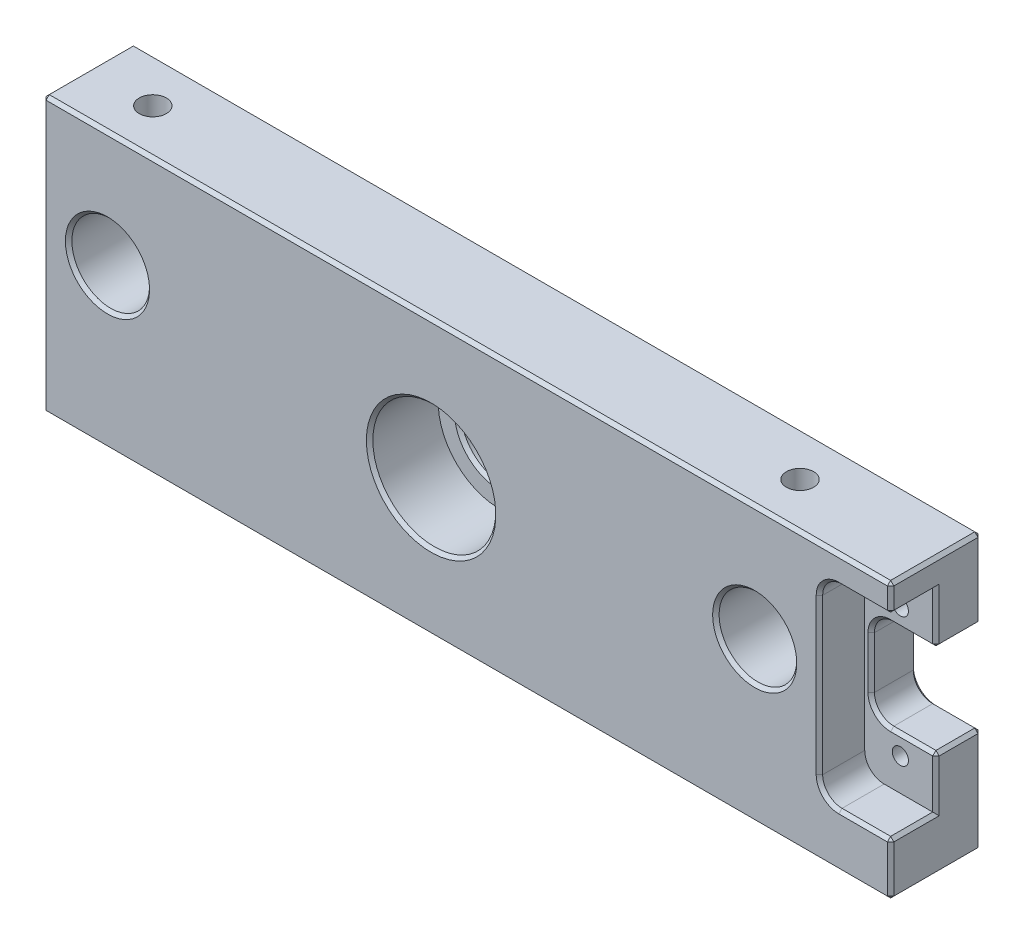
SolidWorks part; units mm, degrees
ref_plane "Front Plane" through (0, 0, 0) normal (0, 0, 1) x (1, 0, 0)
ref_plane "Top Plane" through (0, 0, 0) normal (0, 1, 0) x (1, 0, 0)
ref_plane "Right Plane" through (0, 0, 0) normal (1, 0, 0) x (0, 0, -1)
sketch "Sketch1" plane through (0, 0, 0) normal (0, 0, 1) x (1, 0, 0)
  line L1 (-60, -21.25) -> (60, -21.25)
  line L2 (-60, -21.25) -> (-60, 21.25)
  line L3 (-60, 21.25) -> (60, 21.25)
  line L4 (60, -21.25) -> (60, 21.25)
  line L5 (-60, -21.25) -> (60, 21.25) construction
  line L6 (-60, 21.25) -> (60, -21.25) construction
  point P0 (0, 0)
  dimension "D1" = 120
  dimension "D2" = 42.5
extrude "Boss-Extrude1" add sketch "Sketch1" along normal mid plane 14
sketch "Sketch2" plane through (0, 0, 7) normal (0, 0, 1) x (1, 0, 0)
  circle A0 centre (0, 0) radius 9.5
  dimension "D1" = 19
extrude "Cut-Extrude1" cut sketch "Sketch2" against normal blind 10.6
sketch "Sketch3" plane through (0, 0, -3.6) normal (0, 0, 1) x (1, 0, 0)
  circle A0 centre (0, 0) radius 6.5
  dimension "D1" = 13
extrude "Cut-Extrude2" cut sketch "Sketch3" against normal through all
sketch "Sketch5" plane through (0, 0, 7) normal (0, 0, 1) x (1, 0, 0)
  line L0 (-40.6477, 3.4) -> (36.4799, 3.4) construction
  circle A0 centre (-50, 3.4) radius 6
  circle A1 centre (50, 3.4) radius 6
  dimension "D1" = 12
  dimension "D2" = 12
  dimension "D4" = 50
  dimension "D3" = 50
  dimension "D5" = 3.4
extrude "Cut-Extrude4" cut sketch "Sketch5" against normal through all
hole_wizard "M5x0.8 Tapped Hole1" positions "Sketch9" profile "Sketch8" tap size "M5x0.8" standard "ANSI Metric"
sketch "Sketch9" plane through (0, -21.25, 0) normal (0, -1, 0) x (-1, 0, 0)
  line L0 (-1000, 0) -> (49000, 0) construction
  point P2 (22, 0)
  point P6 (50, 0)
  dimension "D1" = 50
  dimension "D2" = 22
sketch "Sketch8" plane through (-22, -21.25, 0) normal (1, 0, 0) x (0, 0, -1)
  line L0 (0, 0) -> (0, 12.0618)
  line L1 (0, 12.0618) -> (2.1, 10.8)
  line L2 (2.1, 10.8) -> (2.1, 0)
  line L5 (2.1, 0) -> (0, 0)
  line L10 (0, 12.0618) -> (-2.1, 10.8) construction
  line L11 (0, -6.35) -> (0, 107.95) construction
  dimension "Tap Drill Dia." = 4.2
  dimension "Tap Drill Depth" = 10.8
  dimension "Drill Angle" = 118
cosmetic thread "Hole Thread1" parameters "D1"=10, "D2"=5
cosmetic thread "Hole Thread3" parameters "D1"=10, "D2"=5
sketch "Sketch19" plane through (0, -21.25, 0) normal (0, -1, 0) x (1, 0, 0)
  circle A0 centre (-36, 0) radius 1.25
  circle A1 centre (-22, 0) radius 2.1 construction
  dimension "D1" = 2.5
  dimension "D2" = 14
extrude "Cut-Extrude7" cut sketch "Sketch19" against normal blind 10
mirror "Mirror1" about plane through (0, 0, 0) normal (1, 0, 0) of "Cut-Extrude7", "M5x0.8 Tapped Hole1"
hole_wizard "M5x0.8 Tapped Hole2" positions "Sketch11" profile "Sketch10" tap size "M5x0.8" standard "ANSI Metric"
sketch "Sketch11" plane through (0, 21.25, 0) normal (0, 1, 0) x (1, 0, 0)
  line L0 (-1000, 0) -> (49000, 0) construction
  line L3 (-60, -7) -> (-60, 7) construction
  point P0 (-50, 0)
  point P2 (50, 0)
  dimension "D1" = 10
  dimension "D2" = 10
sketch "Sketch10" plane through (-50, 21.25, 0) normal (1, 0, 0) x (0, 0, 1)
  line L0 (0, 0) -> (0, 11.85)
  line L1 (0, 11.85) -> (2.1, 11.85)
  line L2 (2.1, 11.85) -> (2.1, 0)
  line L5 (2.1, 0) -> (0, 0)
  line L11 (0, -6.35) -> (0, 107.95) construction
  dimension "Thru Tap Drill Dia." = 4.2
  dimension "Thru Tap Drill Depth" = 11.85
cosmetic thread "Hole Thread4" parameters "D2"=5
cosmetic thread "Hole Thread5" parameters "D2"=5
sketch "Sketch14" plane through (60, 0, 0) normal (1, 0, 0) x (0, 0, -1)
  line L1 (-7, 21.25) -> (7, 21.25)
  line L2 (-7, 21.25) -> (-7, -21.25)
  line L3 (-7, -21.25) -> (7, -21.25)
  line L4 (7, 21.25) -> (7, -21.25)
extrude "Boss-Extrude2" add sketch "Sketch14" along normal blind 11
sketch "Sketch15" plane through (0, 0, 7) normal (0, 0, 1) x (1, 0, 0)
  line L0 (71, 21.25) -> (71, -21.25) construction
  line L1 (71, 17) -> (60, 17)
  line L2 (71, 17) -> (71, -13)
  line L3 (71, -13) -> (60, -13)
  line L4 (60, 17) -> (60, -13)
  dimension "D1" = 30
  dimension "D2" = 11
  dimension "D3" = 17
extrude "Cut-Extrude5" cut sketch "Sketch15" against normal blind 7
sketch "Sketch16" plane through (0, 0, 0) normal (0, 0, 1) x (1, 0, 0)
  line L0 (71, -13) -> (71, 17) construction
  line L1 (71, 9) -> (61, 9)
  line L2 (71, 9) -> (71, -5)
  line L3 (71, -5) -> (61, -5)
  line L4 (61, 9) -> (61, -5)
  line L5 (60, 2) -> (71, 2) construction
  line L6 (60, 17) -> (60, -13) construction
  dimension "D1" = 14
  dimension "D2" = 7
  dimension "D3" = 10
extrude "Cut-Extrude6" cut sketch "Sketch16" against normal through all
fillet "Fillet1" radius 3 4 edges at (60, -13, 3.5) (60, 17, 3.5) (61, 9, -3.5) (61, -5, -3.5)
hole_wizard "M3x0.5 Tapped Hole1" positions "Sketch18" profile "Sketch17" tap size "M3x0.5" standard "ANSI Metric" end condition through all
sketch "Sketch18" plane through (0, 0, 0) normal (0, 0, 1) x (1, 0, 0)
  line L3 (71, 17) -> (63, 17) construction
  line L4 (65.5, 12) -> (65.5, -8)
  line L6 (71, 9) -> (71, 17) construction
  point P0 (65.5, 12)
  point P2 (65.5, -8)
  point P14 (67, 17)
  dimension "D1" = 5
  dimension "D2" = 20
  dimension "D3" = 5.5
sketch "Sketch17" plane through (65.5, 12, 0) normal (1, 0, 0) x (0, -1, 0)
  line L0 (0, 0) -> (0, 7)
  line L1 (0, 7) -> (1.25, 7)
  line L2 (1.25, 7) -> (1.25, 0)
  line L5 (1.25, 0) -> (0, 0)
  line L11 (0, -6.35) -> (0, 107.95) construction
  dimension "Thru Tap Drill Dia." = 2.5
  dimension "Thru Tap Drill Depth" = 7
cosmetic thread "Hole Thread8" parameters "D2"=3
cosmetic thread "Hole Thread9" parameters "D2"=3
chamfer "Chamfer1" distance 0.5 angle 45 42 edges at (56, 3.4, -7) (-44, 3.4, -7) (6.5, 0, -7) (-44, 3.4, 7) (6.5, 0, -3.6) (9.5, 0, 7) (56, 3.4, 7) (-60, -21.25, 0) (-60, 0, -7) (5.5, -21.25, -7) (5.5, -21.25, 7) (-60, 0, 7) (5.5, 21.25, -7) (-60, 21.25, 0) (5.5, 21.25, 7) (67.5, -5, -7) (61.8787, -4.1213, -7) (61, 2, -7) (61.8787, 8.1213, -7) (67.5, 9, -7) (71, -5, -3.5) (71, 9, -3.5) (71, 15.125, -7) (71, 21.25, 0) (71, 19.125, 7) (71, -13.125, -7) (71, -21.25, 0) (71, -13, 3.5) (71, -9, 0) (67.5, -5, 0) (61.8787, -4.1213, 0) (61, 2, 0) (61.8787, 8.1213, 0) (67.5, 9, 0) (71, 13, 0) (71, 17, 3.5) (67, 17, 7) (60.8787, 16.1213, 7) (60, 2, 7) (60.8787, -12.1213, 7) (67, -13, 7) (71, -17.125, 7)
hole_wizard "M2x0.4 Tapped Hole1" [suppressed] positions "Sketch13" profile "Sketch12" tap size "M2x0.4" standard "ANSI Metric"
sketch "Sketch13" plane through (0, 21.25, 0) normal (0, 1, 0) x (1, 0, 0)
  point P0 (40, 0)
  point P2 (33.5, 0)
  dimension "D1" = 40
  dimension "D2" = 33.5
sketch "Sketch12" plane through (40, 21.25, 0) normal (1, 0, 0) x (0, 0, 1)
  line L0 (0, 0) -> (0, 6.4807)
  line L1 (0, 6.4807) -> (0.8, 6)
  line L2 (0.8, 6) -> (0.8, 0)
  line L5 (0.8, 0) -> (0, 0)
  line L10 (0, 6.4807) -> (-0.8, 6) construction
  line L11 (0, -6.35) -> (0, 107.95) construction
  dimension "Tap Drill Dia." = 1.6
  dimension "Tap Drill Depth" = 6
  dimension "Drill Angle" = 118
cosmetic thread "Hole Thread6" [suppressed] parameters "D1"=4, "D2"=2
cosmetic thread "Hole Thread7" [suppressed] parameters "D1"=4, "D2"=2
equation "\"D2@Sketch16\"=\"D1@Sketch16\"/2"
